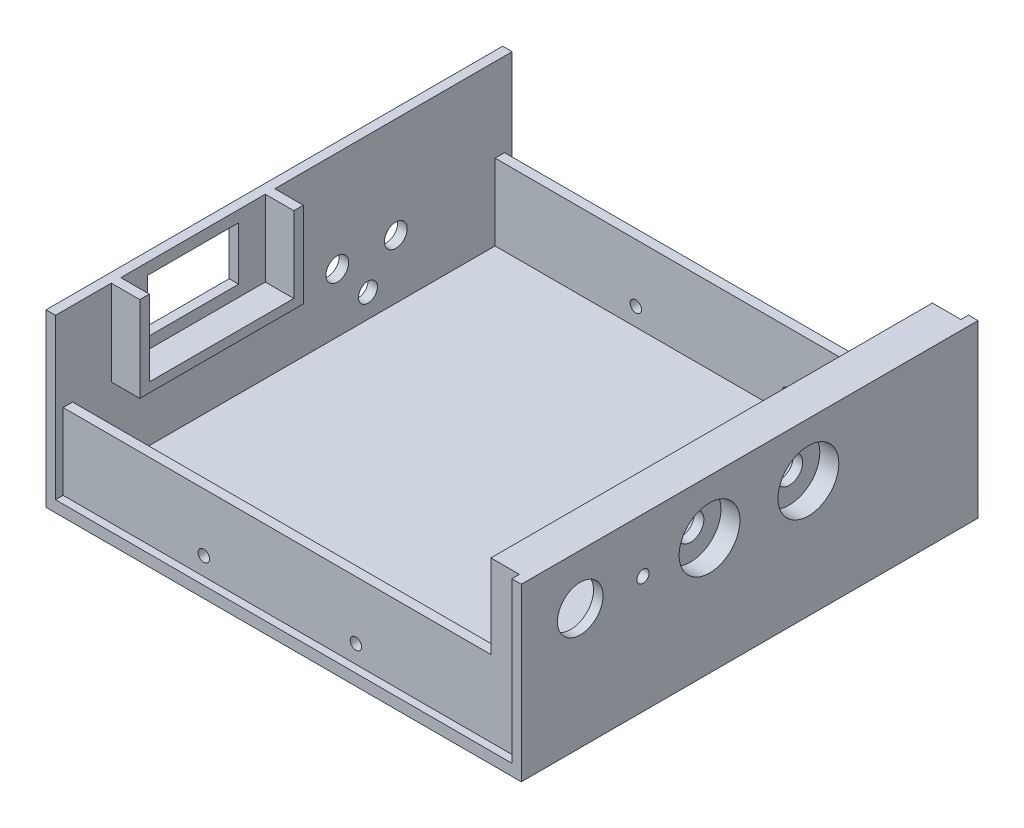
SolidWorks part; units mm, degrees
ref_plane "Front Plane" through (0, 0, 0) normal (0, 0, 1) x (1, 0, 0)
ref_plane "Top Plane" through (0, 0, 0) normal (0, 1, 0) x (1, 0, 0)
ref_plane "Right Plane" through (0, 0, 0) normal (1, 0, 0) x (0, 0, -1)
sketch "Sketch2" plane through (0, 0, 0) normal (0, 1, 0) x (1, 0, 0)
  line L1 (-62.5, -60.05) -> (62.5, -60.05)
  line L2 (-62.5, -60.05) -> (-62.5, 60.05)
  line L3 (-62.5, 60.05) -> (62.5, 60.05)
  line L4 (62.5, -60.05) -> (62.5, 60.05)
  line L5 (-62.5, -60.05) -> (62.5, 60.05) construction
  line L6 (-62.5, 60.05) -> (62.5, -60.05) construction
  point P0 (0, 0)
  dimension "D1" = 120.1
  dimension "D2" = 125
extrude "Boss-Extrude1" add sketch "Sketch2" along normal blind 45
ref_plane "Plane1" through (0, 3, 0) normal (0, 1, 0) x (1, 0, 0)
sketch "Sketch3" plane through (0, 3, 0) normal (0, 1, 0) x (1, 0, 0)
  line L1 (-60, 55.55) -> (60, 55.55)
  line L2 (-60, 55.55) -> (-60, -55.55)
  line L3 (-60, -55.55) -> (60, -55.55)
  line L4 (60, 55.55) -> (60, -55.55)
  line L5 (-60, 55.55) -> (60, -55.55) construction
  line L6 (-60, -55.55) -> (60, 55.55) construction
  point P0 (0, 0)
  dimension "D1" = 111.1
  dimension "D2" = 120
extrude "Cut-Extrude1" cut sketch "Sketch3" along normal blind 39
sketch "Sketch4" plane through (0, 3, 0) normal (0, 1, 0) x (1, 0, 0)
  line L0 (-60.6349, -58.05) -> (86.3959, -58.05) construction
  line L1 (-62.5, -60.05) -> (62.5, -60.05) construction
  line L3 (-60, -58.05) -> (-60, -60.05)
  line L4 (60, -58.05) -> (60, -60.05)
  line L5 (-62.5, 60.05) -> (-62.5, -60.05) construction
  line L6 (62.5, -60.05) -> (62.5, 60.05) construction
  line L7 (-60, -58.05) -> (60, -58.05)
  line L8 (-60, -60.05) -> (60, -60.05)
  dimension "D1" = 2
  dimension "D2" = 2.5
  dimension "D3" = 2.5
extrude "Cut-Extrude3" cut sketch "Sketch4" along normal through all
pattern_linear "LPattern1" count 2 spacing 118.1 along (0, 0, -1) of "Cut-Extrude3"
ref_plane "Plane2" through (0, 23, 0) normal (0, 1, 0) x (1, 0, 0)
sketch "Sketch9" plane through (0, 23, 0) normal (0, 1, 0) x (1, 0, 0)
  line L1 (-60, 58.05) -> (-60, -58.05)
  line L2 (-60, -58.05) -> (52.5, -58.05)
  line L3 (60, -58.05) -> (-60, -58.05) construction
  line L4 (52.5, -58.05) -> (52.5, 58.05)
  line L5 (-60, 58.05) -> (60, 58.05) construction
  line L6 (52.5, 58.05) -> (-60, 58.05)
  line L7 (-62.5, 60.05) -> (-62.5, -60.05) construction
  dimension "D1" = 2.5
  dimension "D2" = 116.1
  dimension "D3" = 7.5
extrude "Cut-Extrude6" cut sketch "Sketch9" along normal through all
ref_plane "Plane3" through (-60, 0, 0) normal (1, 0, 0) x (0, 0, -1)
sketch "Sketch11" plane through (-60, 0, 0) normal (1, 0, 0) x (0, 0, -1)
  line L0 (-71.7709, 18.51) -> (75.8334, 18.51) construction
  line L1 (66.055, 3) -> (-66.055, 3) construction
  line L2 (29.45, 57.4042) -> (29.45, -10.8459) construction
  line L3 (60.05, 45) -> (60.05, 0) construction
  circle A0 centre (29.45, 18.51) radius 3
  circle A1 centre (14.05, 18.51) radius 3
  dimension "D3" = 6
  dimension "D5" = 6
  dimension "D1" = 15.51
  dimension "D2" = 30.6
  dimension "D4" = 15.4
extrude "Cut-Extrude7" cut sketch "Sketch11" against normal through all
sketch "Sketch13" plane through (-60, 0, 0) normal (1, 0, 0) x (0, 0, -1)
  line L0 (20.2396, 28) -> (-44.0105, 28) construction
  line L1 (-19.6354, 28) -> (-19.6354, 69.0313) construction
  line L2 (-60.05, 45) -> (60.05, 45) construction
  line L3 (-35.8854, 42) -> (-11.8854, 42)
  line L4 (-35.8854, 42) -> (-35.8854, 28)
  line L5 (-35.8854, 28) -> (-11.8854, 28)
  line L6 (-11.8854, 42) -> (-11.8854, 28)
  dimension "D1" = 24
  dimension "D2" = 14
  dimension "D3" = 3
sketch "Sketch15" plane through (-60, 0, 0) normal (1, 0, 0) x (0, 0, -1)
  circle A0 centre (22.1174, 9.1984) radius 2.5
  dimension "D1" = 5
extrude "Cut-Extrude9" cut sketch "Sketch15" against normal through all
extrude "Cut-Extrude10" cut sketch "Sketch13" against normal through all
sketch "Sketch17" plane through (-60, 0, 0) normal (1, 0, 0) x (0, 0, -1)
  line L0 (-42.8854, 45) -> (-42.8854, 25)
  line L1 (60.05, 45) -> (-60.05, 45) construction
  line L2 (-42.8854, 25) -> (-4.8854, 25)
  line L3 (-4.8854, 25) -> (-4.8854, 45)
  line L4 (-4.8854, 45) -> (-2.3854, 45)
  line L5 (-2.3854, 45) -> (-2.3854, 22.5)
  line L6 (-2.3854, 22.5) -> (-45.3854, 22.5)
  line L7 (-45.3854, 22.5) -> (-45.3854, 45)
  line L8 (-45.3854, 45) -> (-42.8854, 45)
  line L9 (-11.8854, 28) -> (-11.8854, 42) construction
  line L10 (-35.8854, 42) -> (-35.8854, 28) construction
  line L11 (-35.8854, 28) -> (-11.8854, 28) construction
  dimension "D1" = 2.5
  dimension "D2" = 2.5
  dimension "D3" = 7
  dimension "D4" = 7
  dimension "D5" = 3
  dimension "D6" = 2.5
extrude "Boss-Extrude3" add sketch "Sketch17" along normal blind 7.5
ref_plane "Plane4" through (62.5, 0, 0) normal (1, 0, 0) x (0, 0, -1)
sketch "Sketch18" plane through (62.5, 0, 0) normal (1, 0, 0) x (0, 0, -1)
  line L0 (-60.05, 30.8014) -> (60.05, 30.8014) construction
  line L1 (-60.05, 45) -> (-60.05, 0) construction
  line L2 (60.05, 45) -> (60.05, 0) construction
  line L3 (7.45, 30.8014) -> (7.45, 14.8014)
  line L4 (7.45, 14.8014) -> (4.95, 14.8014)
  line L5 (4.95, 14.8014) -> (4.95, 30.8014)
  line L6 (25.95, 30.8014) -> (25.95, 14.8014)
  line L7 (25.95, 14.8014) -> (23.45, 14.8014)
  line L8 (23.45, 14.8014) -> (23.45, 30.8014)
  arc A0 (7.45, 30.8014) -> (23.45, 30.8014) centre (15.45, 30.8014) cw
  arc A2 (4.95, 30.8014) -> (25.95, 30.8014) centre (15.45, 30.8014) cw
  dimension "D1" = 16
  dimension "D3" = 2.5
  dimension "D4" = 65
  dimension "D5" = 16
  dimension "D6" = 16
extrude "Boss-Extrude4" add sketch "Sketch18" against normal blind 10 contours L8 A0 L3 L4 L5 A2 L6 L7
pattern_linear "LPattern3" count 2 spacing 26 along (0, 0, 1) of "Boss-Extrude4"
sketch "Sketch22" plane through (62.5, 0, 0) normal (1, 0, 0) x (0, 0, -1)
  circle A0 centre (15.45, 30.8014) radius 3.5
  dimension "D1" = 7
extrude "Cut-Extrude11" cut sketch "Sketch22" against normal blind 10
pattern_linear "LPattern4" count 2 spacing 26 along (0, 0, 1) of "Cut-Extrude11"
sketch "Sketch23" plane through (62.5, 0, 0) normal (1, 0, 0) x (0, 0, -1)
  line L0 (-60.05, 30.8014) -> (70.1426, 30.8014) construction
  line L1 (-21.05, 30.8014) -> (-21.05, 14.8014) construction
  circle A0 centre (-28.05, 30.8014) radius 1.6
  dimension "D1" = 3.2
  dimension "D2" = 7
extrude "Cut-Extrude12" cut sketch "Sketch23" against normal blind 10
sketch "Sketch26" plane through (62.5, 0, 0) normal (1, 0, 0) x (0, 0, -1)
  line L0 (23.45, 14.8014) -> (7.45, 14.8014)
  line L1 (7.45, 14.8014) -> (7.45, 30.8014)
  line L2 (23.45, 30.8014) -> (23.45, 14.8014)
  circle A0 centre (15.45, 30.8014) radius 3.5
  arc A1 (7.45, 30.8014) -> (23.45, 30.8014) centre (15.45, 30.8014) cw
extrude "Boss-Extrude10" add sketch "Sketch26" against normal blind 7.5
pattern_linear "LPattern9" count 2 spacing 26 along (0, 0, 1) of "Boss-Extrude10"
sketch "Sketch27" plane through (62.5, 0, 0) normal (1, 0, 0) x (0, 0, -1)
  circle A0 centre (-44.5522, 31.7096) radius 6
extrude "Cut-Extrude13" cut sketch "Sketch27" against normal blind 7.5
sketch "Sketch28" plane through (0, 0, 0) normal (0, 0, 1) x (1, 0, 0)
  line L0 (-64.0816, 7.75) -> (75.8762, 7.75) construction
  line L1 (-60, 45) -> (-60, 3) construction
  line L2 (-60, 3) -> (60, 3) construction
  circle A0 centre (-23, 7.75) radius 1.5
  circle A1 centre (17, 7.75) radius 1.5
  dimension "D1" = 3
  dimension "D2" = 3
  dimension "D3" = 40
  dimension "D4" = 37
  dimension "D5" = 4.75
extrude "Cut-Extrude14" cut sketch "Sketch28" against normal through all and the other way through all
sketch "Sketch30" plane through (62.5, 0, 0) normal (1, 0, 0) x (0, 0, -1)
  circle A0 centre (15.45, 30.8014) radius 8
extrude "Cut-Extrude15" cut sketch "Sketch30" against normal blind 5
pattern_linear "LPattern10" count 2 spacing 26 along (0, 0, 1) of "Cut-Extrude15"
